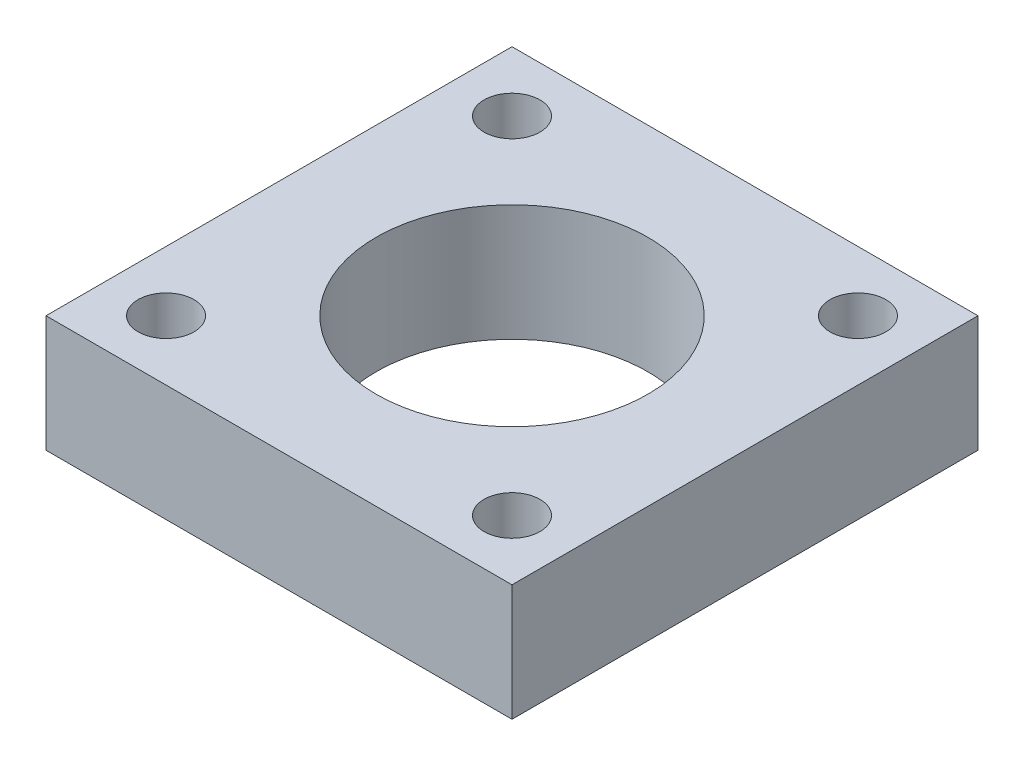
SolidWorks part; units mm, degrees
ref_plane "Front Plane" through (0, 0, 0) normal (0, 0, 1) x (1, 0, 0)
ref_plane "Top Plane" through (0, 0, 0) normal (0, 1, 0) x (1, 0, 0)
ref_plane "Right Plane" through (0, 0, 0) normal (1, 0, 0) x (0, 0, -1)
sketch "Sketch1" plane through (0, 0, 0) normal (0, 1, 0) x (1, 0, 0)
  line L0 (14.1421, 14.1421) -> (14.1421, -14.1421) construction
  line L1 (-19.05, -19.05) -> (19.05, -19.05)
  line L2 (-19.05, -19.05) -> (-19.05, 19.05)
  line L3 (-19.05, 19.05) -> (19.05, 19.05)
  line L4 (19.05, -19.05) -> (19.05, 19.05)
  line L5 (-19.05, -19.05) -> (19.05, 19.05) construction
  line L6 (-19.05, 19.05) -> (19.05, -19.05) construction
  circle A0 centre (14.1421, 14.1421) radius 2.286
  circle A1 centre (14.1421, -14.1421) radius 2.286
  circle A2 centre (-14.1421, -14.1421) radius 2.286
  circle A3 centre (-14.1421, 14.1421) radius 2.286
  circle A4 centre (0, 0) radius 11.1125
  point P0 (0, 0)
  point P18 (0, 0)
  dimension "D2" = 4.572
  dimension "D4" = 40
  dimension "D5" = 22.225
  dimension "D1" = 38.1
  dimension "D3" = 4
extrude "Boss-Extrude1" add sketch "Sketch1" along normal blind 9.525
